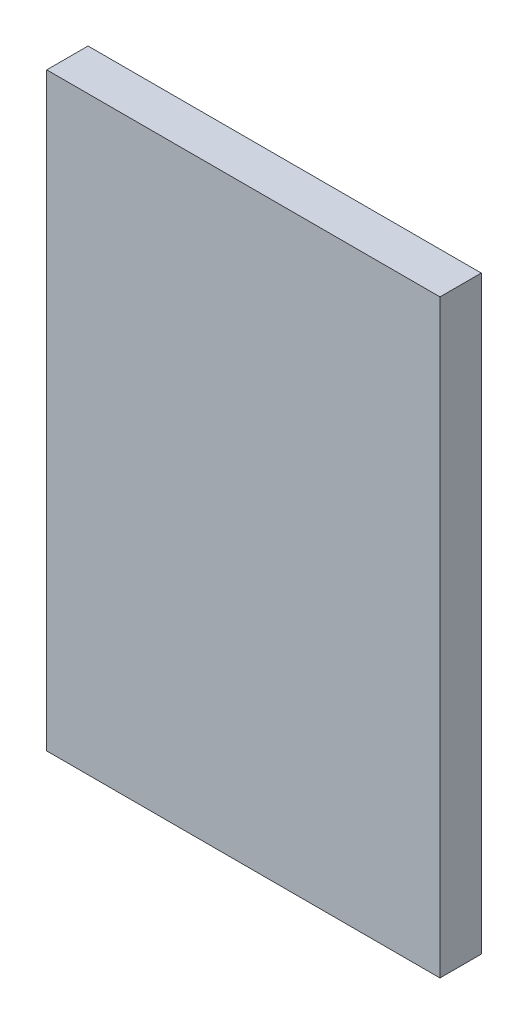
SolidWorks part; units mm, degrees
ref_plane "Front Plane" through (0, 0, 0) normal (0, 0, 1) x (1, 0, 0)
ref_plane "Top Plane" through (0, 0, 0) normal (0, 1, 0) x (1, 0, 0)
ref_plane "Right Plane" through (0, 0, 0) normal (1, 0, 0) x (0, 0, -1)
sketch "Sketch1" plane through (0, 0, 0) normal (0, 0, 1) x (1, 0, 0)
  line L1 (0, 0) -> (200, 0)
  line L2 (0, 0) -> (0, 300)
  line L3 (0, 300) -> (200, 300)
  line L4 (200, 0) -> (200, 300)
extrude "Boss-Extrude1" add sketch "Sketch1" along normal blind 21
